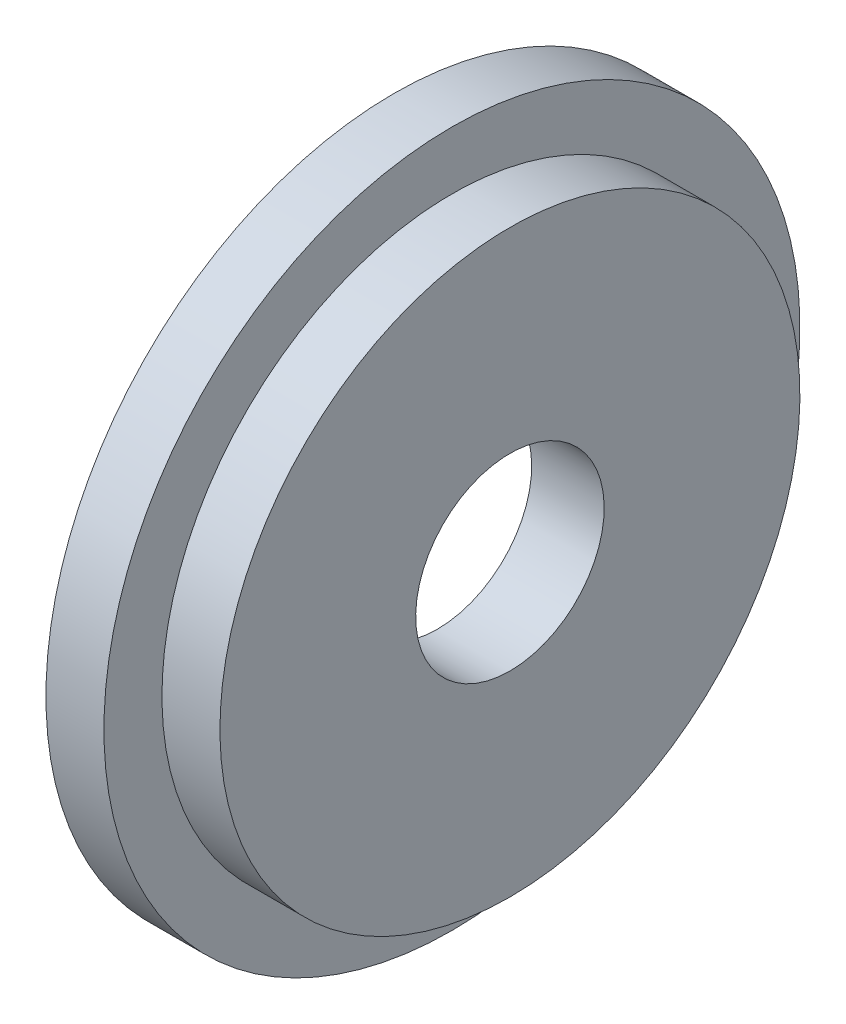
SolidWorks part; units mm, degrees
material "AISI 1020"
ref_plane "Спереди" through (0, 0, 0) normal (0, 0, 1) x (1, 0, 0)
ref_plane "Сверху" through (0, 0, 0) normal (0, 1, 0) x (1, 0, 0)
ref_plane "Справа" through (0, 0, 0) normal (1, 0, 0) x (0, 0, -1)
sketch "Эскиз1" plane through (0, 0, 0) normal (0, 0, 1) x (1, 0, 0)
  line L1 (-4.4802, 8.5) -> (-4.4802, 12)
  line L2 (-4.4802, 12) -> (-2.4802, 12)
  line L3 (-2.4802, 12) -> (-2.4802, 10)
  line L4 (-2.4802, 10) -> (-0.4802, 10)
  line L5 (-0.4802, 10) -> (-0.4802, 3.25)
  line L6 (-2.9802, 3.25) -> (-0.4802, 3.25)
  line L7 (-2.4802, 0) -> (-4.4802, 0) construction
  line L8 (-4.4802, 0) -> (-0.4802, 0) construction
  line L9 (-4.4802, 8.5) -> (-2.9802, 8.5)
  line L10 (-2.9802, 8.5) -> (-2.9802, 3.25)
  dimension "D1" = 3.25
  dimension "D2" = 1.5
  dimension "D3" = 17
revolve "Повернуть1" add sketch "Эскиз1" angle 360 about L8
